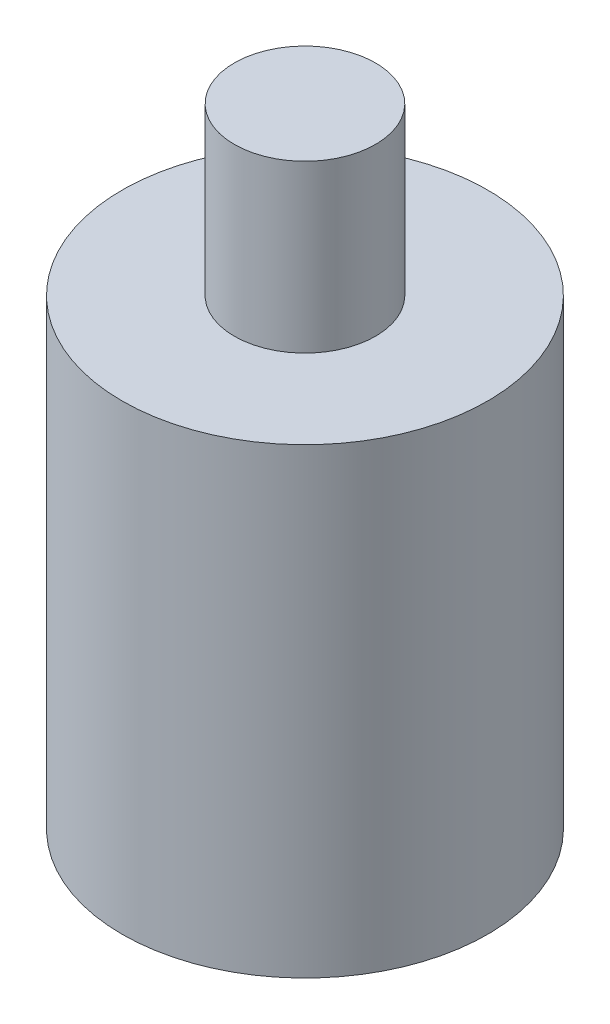
SolidWorks part; units mm, degrees
material "AISI 1020"
ref_plane "Front Plane" through (0, 0, 0) normal (0, 0, 1) x (1, 0, 0)
ref_plane "Top Plane" through (0, 0, 0) normal (0, 1, 0) x (1, 0, 0)
ref_plane "Right Plane" through (0, 0, 0) normal (1, 0, 0) x (0, 0, -1)
sketch "Sketch1" plane through (0, 0, 0) normal (0, 1, 0) x (1, 0, 0)
  circle A0 centre (0, 0) radius 110
  dimension "D1" = 220
extrude "Boss-Extrude1" add sketch "Sketch1" along normal blind 278
sketch "Sketch2" plane through (0, 278, 0) normal (0, 1, 0) x (1, 0, 0)
  circle A0 centre (0, 0) radius 42.5
  dimension "D1" = 85
extrude "Boss-Extrude2" add sketch "Sketch2" along normal blind 100
